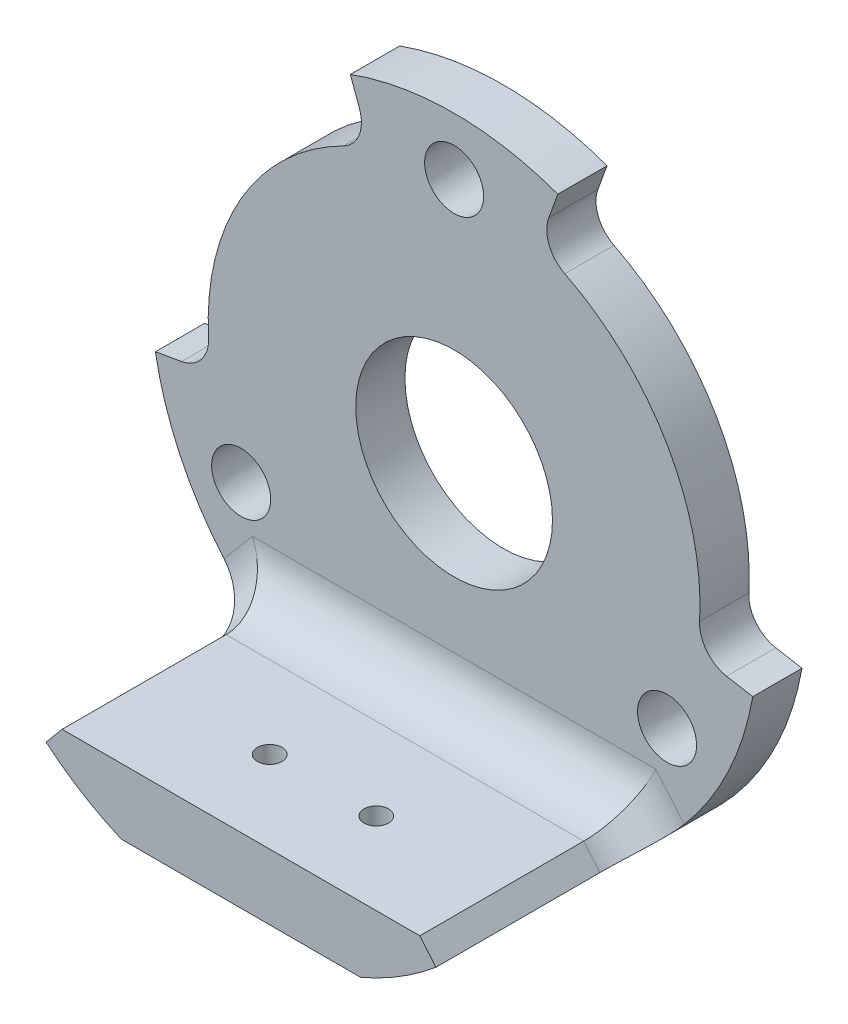
SolidWorks part; units mm, degrees
ref_plane "前视基准面" through (0, 0, 0) normal (0, 0, 1) x (1, 0, 0)
ref_plane "上视基准面" through (0, 0, 0) normal (0, 1, 0) x (1, 0, 0)
ref_plane "右视基准面" through (0, 0, 0) normal (1, 0, 0) x (0, 0, -1)
ref_plane "基准面4" through (0, 0, 0) normal (0, 0, -1) x (-1, 0, 0)
sketch "草图1" plane through (0, 0, 0) normal (0, 0, -1) x (-1, 0, 0)
  line L0 (442.7027, 283) -> (457.2973, 283)
  arc A0 (457.2973, 283) -> (442.7027, 283) centre (450, 300) ccw
extrude "凸台-拉伸1" add sketch "草图1" against normal blind 16
sketch "草图2" plane through (0, 0, 16) normal (0, 0, 1) x (1, 0, 0)
  line L0 (-461.8916, 285.8282) -> (-460.9083, 287)
  line L1 (-460.9083, 287) -> (-439.0917, 287)
  line L2 (-439.0917, 287) -> (-438.1084, 285.8282)
  arc A0 (-438.1084, 285.8282) -> (-461.8916, 285.8282) centre (-450, 300) ccw
extrude "切除-拉伸1" cut sketch "草图2" against normal blind 13
sketch "草图3" plane through (0, 0, 0) normal (0, 0, -1) x (-1, 0, 0)
  line L0 (431.7811, 296.7875) -> (435.2279, 297.3953)
  line L1 (444.8697, 314.0954) -> (443.6726, 317.3843)
  arc A0 (435.2279, 297.3953) -> (444.8697, 314.0954) centre (450, 300) cw
  arc A1 (443.6726, 317.3843) -> (431.7811, 296.7875) centre (450, 300) ccw
extrude "切除-拉伸2" cut sketch "草图3" against normal through all
sketch "草图4" plane through (0, 0, 0) normal (0, 0, -1) x (-1, 0, 0)
  line L0 (456.3274, 317.3843) -> (455.1303, 314.0954)
  line L1 (464.7721, 297.3953) -> (468.2189, 296.7875)
  arc A0 (455.1303, 314.0954) -> (464.7721, 297.3953) centre (450, 300) cw
  arc A1 (468.2189, 296.7875) -> (456.3274, 317.3843) centre (450, 300) ccw
extrude "切除-拉伸3" cut sketch "草图4" against normal through all
hole_wizard "Ø1.5 (1.5) 直径孔1" positions "草图6" profile "草图5" hole size "Ø1.5" standard "ANSI Metric"
sketch "草图6" plane through (0, 283, 0) normal (0, -1, 0) x (-1, 0, 0)
  point P0 (446.75, -11)
  point P1 (453.25, -11)
sketch "草图5" plane through (-446.75, 283, 11) normal (1, 0, 0) x (0, 0, -1)
  line L0 (0, 0) -> (0, 35.5)
  line L1 (0, 35.5) -> (0.75, 35.5)
  line L2 (0.75, 35.5) -> (0.75, 0)
  line L5 (0.75, 0) -> (0, 0)
  line L11 (0, -6.35) -> (0, 107.95) construction
  dimension "通孔孔直径" = 1.5
  dimension "通孔孔深度" = 35.5
hole_wizard "Ø12.0 (12) 直径孔1" positions "草图8" profile "草图7" hole size "Ø12.0" standard "ANSI Metric"
sketch "草图8" plane through (0, 0, 0) normal (0, 0, -1) x (-1, 0, 0)
  point P0 (450, 300)
sketch "草图7" plane through (-450, 300, 0) normal (1, 0, 0) x (0, 1, 0)
  line L0 (0, 0) -> (0, 16)
  line L1 (0, 16) -> (6, 16)
  line L2 (6, 16) -> (6, 0)
  line L5 (6, 0) -> (0, 0)
  line L11 (0, -6.35) -> (0, 107.95) construction
  dimension "通孔孔直径" = 12
  dimension "通孔孔深度" = 16
hole_wizard "Ø3.6 (3.6) 直径孔1" positions "草图10" profile "草图9" hole size "Ø3.6" standard "ANSI Metric"
sketch "草图10" plane through (0, 0, 0) normal (0, 0, -1) x (-1, 0, 0)
  point P0 (437.0096, 292.5)
  point P1 (450, 315)
  point P2 (462.9904, 292.5)
sketch "草图9" plane through (-437.0096, 292.5, 0) normal (1, 0, 0) x (0, 1, 0)
  line L0 (0, 0) -> (0, 16)
  line L1 (0, 16) -> (1.8, 16)
  line L2 (1.8, 16) -> (1.8, 0)
  line L5 (1.8, 0) -> (0, 0)
  line L11 (0, -6.35) -> (0, 107.95) construction
  dimension "通孔孔直径" = 3.6
  dimension "通孔孔深度" = 16
fillet "圆角1" radius 2 4 edges at (-435.2279, 297.3953, 1.5) (-464.7721, 297.3953, 1.5) (-455.1303, 314.0954, 1.5) (-444.8697, 314.0954, 1.5)
fillet "圆角2" radius 3 3 edges at (-438.6001, 286.4141, 3) (-461.3999, 286.4141, 3) (-450, 287, 3)
